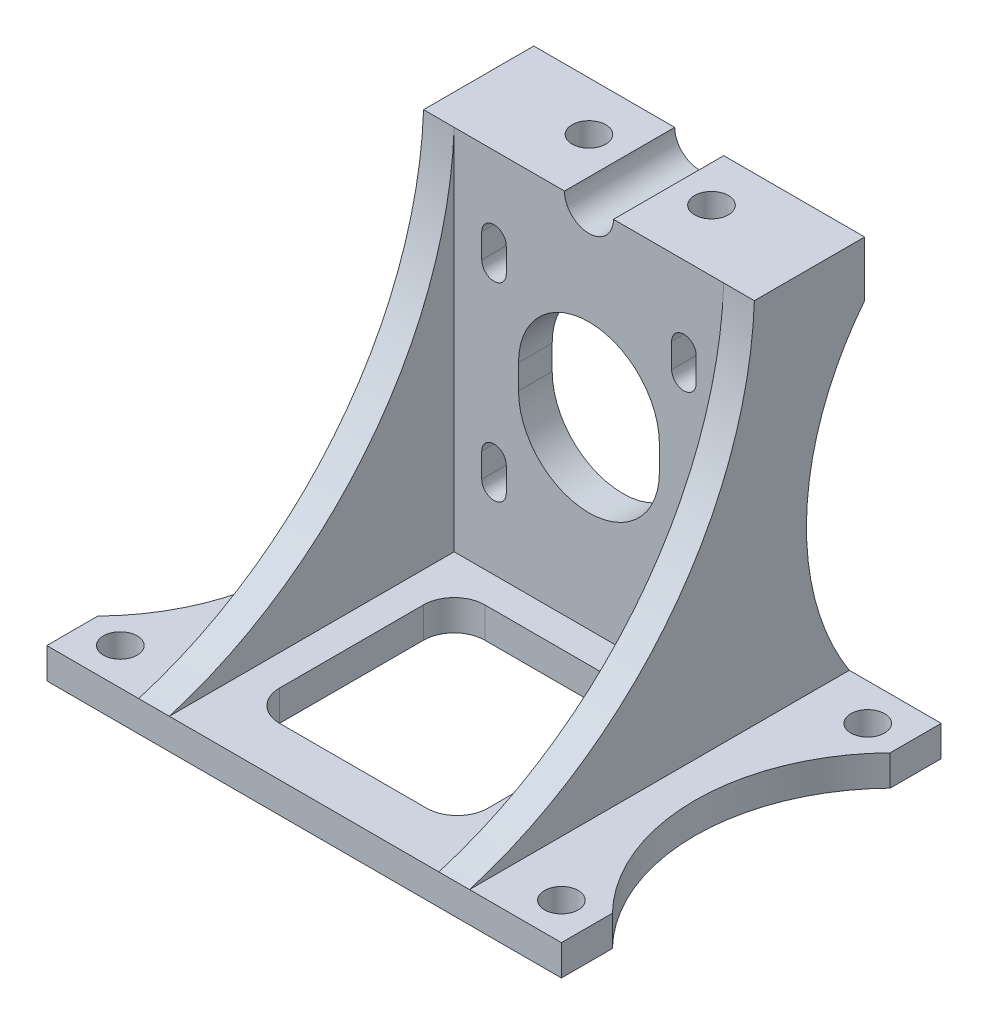
SolidWorks part; units mm, degrees
ref_plane "Front Plane" through (0, 0, 0) normal (0, 0, 1) x (1, 0, 0)
ref_plane "Top Plane" through (0, 0, 0) normal (0, 1, 0) x (1, 0, 0)
ref_plane "Right Plane" through (0, 0, 0) normal (1, 0, 0) x (0, 0, -1)
sketch "Sketch1" plane through (0, 0, 0) normal (0, 0, 1) x (1, 0, 0)
  line L0 (-42, 0) -> (42, 0)
  line L1 (42, 0) -> (42, 5)
  line L2 (42, 5) -> (27, 5)
  line L3 (27, 5) -> (27, 65)
  line L4 (27, 65) -> (4, 65)
  line L5 (-27, 65) -> (-27, 5)
  line L6 (-27, 5) -> (-42, 5)
  line L7 (-42, 5) -> (-42, 0)
  line L8 (-4, 65) -> (-27, 65)
  line L9 (0, 65) -> (0, 0) construction
  line L10 (-4, 65) -> (4, 65) construction
  line L11 (-11.5, 37) -> (-11.5, 33)
  line L12 (11.5, 37) -> (11.5, 33)
  arc A0 (-4, 65) -> (4, 65) centre (0, 65) ccw
  arc A1 (-11.5, 33) -> (11.5, 33) centre (0, 33) ccw
  arc A2 (11.5, 37) -> (-11.5, 37) centre (0, 37) ccw
  dimension "D5" = 8
  dimension "D7" = 23
  dimension "D8" = 4
  dimension "D1" = 54
  dimension "D2" = 84
  dimension "D3" = 5
  dimension "D4" = 65
  dimension "D6" = 33
extrude "Boss-Extrude1" add sketch "Sketch1" along normal blind 62
sketch "Sketch2" plane through (-42, 0, 0) normal (-1, 0, 0) x (0, 0, 1)
  line L0 (62, 65) -> (0, 65) construction
  line L1 (10, 65) -> (0, 65)
  line L2 (10, 65) -> (10, 5)
  line L3 (62, 5) -> (62, 65)
  line L4 (10, 5) -> (0, 5)
  line L5 (15.5, 65) -> (62, 65)
  line L6 (0, 65) -> (0, 5) construction
  line L7 (62, 65) -> (0, 65) construction
  line L8 (0, 65) -> (0, 5)
  arc A0 (15.5, 65) -> (62, 5) centre (80.4584, 67.324) ccw
  dimension "D2" = 5.5
  dimension "D3" = 65
  dimension "D1" = 15.5
extrude "Cut-Extrude1" cut sketch "Sketch2" against normal through all
sketch "Sketch12" plane through (0, 5, 0) normal (0, 1, 0) x (1, 0, 0)
  line L1 (-22, -15.5) -> (22, -15.5)
  line L2 (-22, -15.5) -> (-22, -66.6205)
  line L3 (-22, -66.6205) -> (22, -66.6205)
  line L4 (22, -15.5) -> (22, -66.6205)
  line L6 (-27, -15.5) -> (-27, -62) construction
  line L8 (27, -62) -> (27, -15.5) construction
  line L9 (27, -15.5) -> (4, -15.5) construction
  dimension "D1" = 5
  dimension "D2" = 5
extrude "Cut-Extrude11" cut sketch "Sketch12" along normal blind 30
sketch "Sketch17" plane through (0, 5, 0) normal (0, 1, 0) x (1, 0, 0)
  line L0 (-36, -6) -> (36, -56) construction
  line L1 (0, -31) -> (42, -31) construction
  line L2 (42, -62) -> (42, 0) construction
  line L3 (0, -31) -> (0, 0) construction
  line L4 (-42, -62) -> (-42, 0) construction
  circle A0 centre (-36, -6) radius 2.75
  circle A1 centre (36, -6) radius 2.75
  circle A2 centre (36, -56) radius 2.75
  circle A3 centre (-36, -56) radius 2.75
  circle A4 centre (65.2788, -31) radius 32.5
  circle A5 centre (-65.2788, -31) radius 32.5
  dimension "D1" = 5.5
  dimension "D4" = 6
  dimension "D5" = 6
  dimension "D6" = 65
  dimension "D2" = 6
  dimension "D3" = 50
extrude "Cut-Extrude14" cut sketch "Sketch17" against normal through all
sketch "Sketch20" plane through (0, 0, 15.5) normal (0, 0, 1) x (1, 0, 0)
  line L0 (-42, 0) -> (42, 0) construction
  line L1 (-15.5, 52.5) -> (-15.5, 48.5) construction
  line L2 (15.5, 52.5) -> (15.5, 48.5) construction
  line L3 (15.5, 21.5) -> (15.5, 17.5) construction
  line L4 (-15.5, 21.5) -> (-15.5, 17.5) construction
  line L5 (-17.5, 52.5) -> (-17.5, 48.5)
  line L6 (-13.5, 48.5) -> (-13.5, 52.5)
  line L7 (13.5, 52.5) -> (13.5, 48.5)
  line L8 (17.5, 48.5) -> (17.5, 52.5)
  line L9 (-17.5, 21.5) -> (-17.5, 17.5)
  line L10 (-13.5, 17.5) -> (-13.5, 21.5)
  line L11 (13.5, 17.5) -> (13.5, 21.5)
  line L12 (17.5, 21.5) -> (17.5, 17.5)
  arc A0 (-17.5, 48.5) -> (-13.5, 48.5) centre (-15.5, 48.5) ccw
  arc A1 (13.5, 48.5) -> (17.5, 48.5) centre (15.5, 48.5) ccw
  arc A2 (13.5, 17.5) -> (17.5, 17.5) centre (15.5, 17.5) ccw
  arc A3 (-17.5, 17.5) -> (-13.5, 17.5) centre (-15.5, 17.5) ccw
  arc A4 (-13.5, 21.5) -> (-17.5, 21.5) centre (-15.5, 21.5) ccw
  arc A5 (-13.5, 52.5) -> (-17.5, 52.5) centre (-15.5, 52.5) ccw
  arc A6 (17.5, 52.5) -> (13.5, 52.5) centre (15.5, 52.5) ccw
  arc A7 (17.5, 21.5) -> (13.5, 21.5) centre (15.5, 21.5) ccw
  dimension "D3" = 4
  dimension "D1" = 31
  dimension "D2" = 31
  dimension "D4" = 17.5
  dimension "D5" = 15.5
  dimension "D6" = 4
extrude "Cut-Extrude17" cut sketch "Sketch20" against normal blind 10
sketch "Sketch21" plane through (0, 5, 0) normal (0, 1, 0) x (1, 0, 0)
  line L0 (-22, -62) -> (-22, -24.0656) construction
  line L5 (-12, -20.5) -> (12, -20.5)
  line L6 (-17, -25.5) -> (-17, -49)
  line L7 (-12, -54) -> (12, -54)
  line L8 (17, -25.5) -> (17, -49)
  line L9 (22, -15.5) -> (-22, -15.5) construction
  line L13 (22, -62) -> (-22, -62) construction
  line L14 (22, -62) -> (22, -15.5) construction
  arc A4 (-12, -20.5) -> (-17, -25.5) centre (-12, -25.5) ccw
  arc A5 (12, -20.5) -> (17, -25.5) centre (12, -25.5) cw
  arc A6 (12, -54) -> (17, -49) centre (12, -49) ccw
  arc A7 (-17, -49) -> (-12, -54) centre (-12, -49) ccw
  dimension "D3" = 5
  dimension "D1" = 5
  dimension "D2" = 5
  dimension "D5" = 8
  dimension "D6" = 5
extrude "Cut-Extrude18" cut sketch "Sketch21" against normal through all
sketch "Sketch24" plane through (0, 35, 0) normal (0, -1, 0) x (1, 0, 0)
  line L0 (-22, 15.5) -> (-22, 24.0656) construction
  line L1 (-22, 15.5) -> (-22, 24.0656)
  line L4 (11.5, 24.0656) -> (11.5, 15.5)
  line L5 (11.5, 15.5) -> (22, 15.5)
  line L6 (22, 15.5) -> (22, 24.0656)
  line L7 (22, 24.0656) -> (11.5, 24.0656)
  line L9 (-22, 15.5) -> (22, 15.5)
  line L10 (22, 15.5) -> (22, 24.0656)
  line L11 (22, 24.0656) -> (-22, 24.0656)
  dimension "D1" = 0
extrude "Cut-Extrude19" cut sketch "Sketch24" against normal through all
sketch "Sketch25" plane through (0, 0, 10) normal (0, 0, -1) x (-1, 0, 0)
  line L0 (-27, 65) -> (-4, 65) construction
  line L1 (-27, 65) -> (-4, 65)
  line L2 (-27, 65) -> (-27, 56)
  line L3 (-27, 56) -> (27, 56)
  line L4 (27, 65) -> (27, 56)
  line L5 (4, 65) -> (27, 65)
  line L6 (27, 65) -> (27, 5) construction
  arc A1 (-4, 65) -> (4, 65) centre (0, 65) ccw
  arc A2 (-4, 65) -> (4, 65) centre (0, 65) ccw construction
  dimension "D2" = 9
extrude "Boss-Extrude2" add sketch "Sketch25" along normal blind 12.5
sketch "Sketch27" plane through (-27, 0, 0) normal (-1, 0, 0) x (0, 0, 1)
  line L2 (-2.5, 56) -> (10, 56)
  line L3 (10, 56) -> (10, 5)
  line L5 (10, 56) -> (10, 5) construction
  line L6 (-2.5, 56) -> (-2.5, 65) construction
  line L7 (-2.5, 56) -> (10, 56) construction
  line L8 (8.3208, 5) -> (0, 5) construction
  line L9 (10, 5) -> (0, 5)
  arc A0 (0, 5) -> (-2.5, 56) centre (-36.813, 28.7567) ccw
  dimension "D1" = 3
extrude "Boss-Extrude3" add sketch "Sketch27" against normal blind 5
mirror "Mirror1" about plane through (0, 0, 0) normal (1, 0, 0) of "Boss-Extrude3"
sketch "Sketch28" plane through (0, 56, 0) normal (0, -1, 0) x (1, 0, 0)
  line L0 (22, -2.5) -> (-22, -2.5) construction
  line L1 (-5.0925, 5.5) -> (-7.5463, 9.75)
  line L2 (-7.5463, 9.75) -> (-12.4537, 9.75)
  line L3 (-12.4537, 9.75) -> (-14.9075, 5.5)
  line L4 (-14.9075, 5.5) -> (-12.4537, 1.25)
  line L5 (-12.4537, 1.25) -> (-7.5463, 1.25)
  line L6 (-7.5463, 1.25) -> (-5.0925, 5.5)
  line L7 (5.0925, 5.5) -> (7.5463, 1.25)
  line L8 (7.5463, 1.25) -> (12.4537, 1.25)
  line L9 (12.4537, 1.25) -> (14.9075, 5.5)
  line L10 (14.9075, 5.5) -> (12.4537, 9.75)
  line L11 (12.4537, 9.75) -> (7.5463, 9.75)
  line L12 (7.5463, 9.75) -> (5.0925, 5.5)
  line L13 (0, 15.5) -> (0, -2.5) construction
  circle A0 centre (-10, 5.5) radius 4.25 construction
  circle A1 centre (10, 5.5) radius 4.25 construction
  dimension "D4" = 8.5
  dimension "D1" = 8
  dimension "D2" = 20
  dimension "D3" = 10
extrude "Cut-Extrude20" cut sketch "Sketch28" against normal offset from surface (3.4 mm away) 5 from offset 0.6 up to face at (16.8, 65, 8.3) offset against normal yes
sketch "Sketch29" plane through (0, 65, 0) normal (0, 1, 0) x (1, 0, 0)
  line L0 (-10, -5.5) -> (10, -5.5) construction
  line L1 (0, 0) -> (0, -5.5) construction
  line L2 (-27, 2.5) -> (-4, 2.5) construction
  circle A0 centre (-10, -5.5) radius 2.75
  circle A1 centre (10, -5.5) radius 2.75
  dimension "D2" = 5.5
  dimension "D1" = 20
  dimension "D3" = 8
extrude "Cut-Extrude21" cut sketch "Sketch29" against normal blind 6
sketch "Sketch33" plane through (0, 60, 0) normal (0, -1, 0) x (1, 0, 0)
  circle A0 centre (10, 5.5) radius 2.75 construction
  circle A1 centre (-10, 5.5) radius 2.75 construction
  circle A2 centre (10, 5.5) radius 2.75
  circle A3 centre (-10, 5.5) radius 2.75
extrude "Boss-Extrude5" add sketch "Sketch33" against normal blind 0.4
